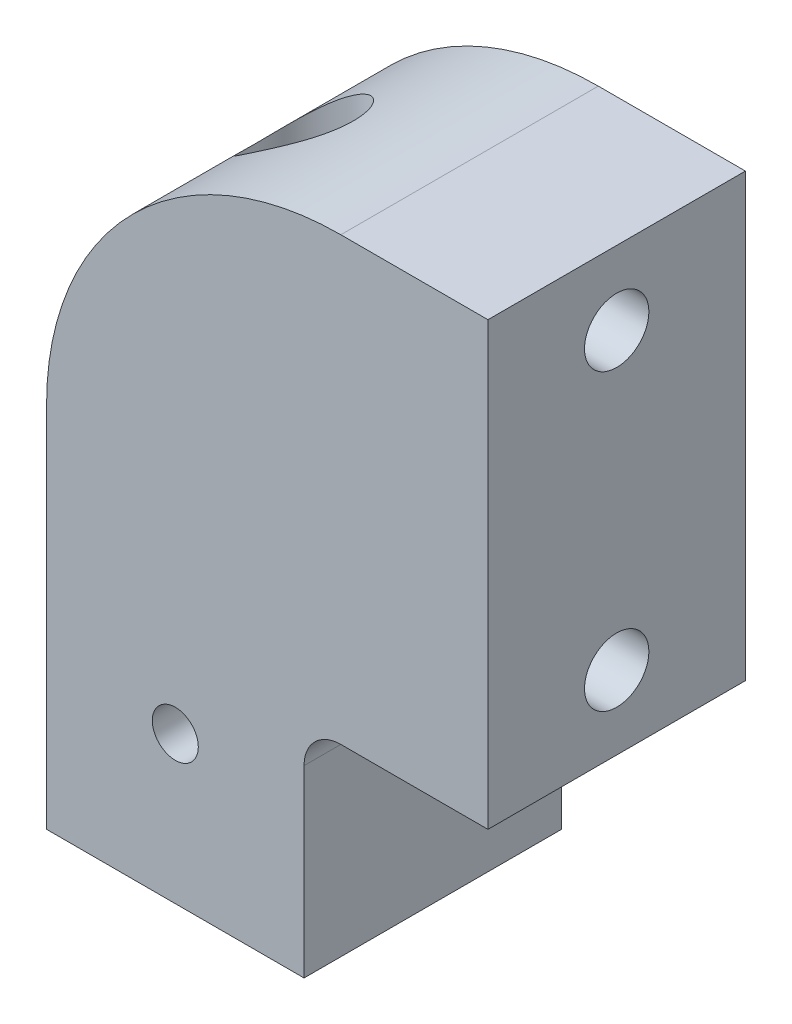
SolidWorks part; units mm, degrees
material "PE High Density"
ref_plane "Front Plane" through (0, 0, 0) normal (0, 0, 1) x (1, 0, 0)
ref_plane "Top Plane" through (0, 0, 0) normal (0, 1, 0) x (1, 0, 0)
ref_plane "Right Plane" through (0, 0, 0) normal (1, 0, 0) x (0, 0, -1)
sketch "Sketch1" plane through (0, 0, 0) normal (0, 0, 1) x (1, 0, 0)
  line L0 (0, 0) -> (0, 57.15)
  line L1 (38.1, 57.15) -> (0, 57.15)
  line L2 (38.1, 57.15) -> (38.1, 19.05)
  line L3 (38.1, 19.05) -> (22.225, 19.05)
  line L4 (22.225, 19.05) -> (22.225, 0)
  line L5 (22.225, 0) -> (0, 0)
  dimension "D1" = 22.225
  dimension "D2" = 19.05
  dimension "D3" = 38.1
  dimension "D4" = 38.1
extrude "Boss-Extrude1" add sketch "Sketch1" along normal blind 22.225
fillet "Fillet1" radius 3.175 1 edges at (22.225, 19.05, 11.1125)
fillet "Fillet2" radius 25.4 1 edges at (0, 57.15, 11.1125)
sketch "Sketch3" plane through (0, 0, 0) normal (0, -1, 0) x (1, 0, 0)
  line L0 (0, 22.225) -> (22.225, 0) construction
  line L1 (0, 0) -> (22.225, 0) construction
  line L2 (22.225, 0) -> (22.225, 22.225) construction
  line L3 (22.225, 22.225) -> (0, 0) construction
  circle A0 centre (11.1125, 11.1125) radius 7.1438
  dimension "D1" = 14.2875
extrude "Cut-Extrude1" cut sketch "Sketch3" against normal blind 9.525
sketch "Sketch4" plane through (0, 0, 0) normal (0, -1, 0) x (1, 0, 0)
  circle A0 centre (11.1125, 11.1125) radius 4.25
  dimension "D1" = 8.5
extrude "Cut-Extrude2" cut sketch "Sketch4" against normal through all
hole_wizard "7/32 (0.21875) Diameter Hole1" positions "Sketch7" profile "Sketch5" hole size "7/32" standard "ANSI Inch"
sketch "Sketch7" plane through (38.1, 0, 0) normal (1, 0, 0) x (0, 0, -1)
  line L0 (-11.1125, 57.15) -> (-11.1125, 19.05) construction
  line L1 (-22.225, 57.15) -> (0, 57.15) construction
  line L2 (-22.225, 19.05) -> (0, 19.05) construction
  line L4 (-22.225, 38.1) -> (0, 38.1) construction
  line L5 (-22.225, 19.05) -> (-22.225, 57.15) construction
  line L6 (0, 19.05) -> (0, 57.15) construction
  point P0 (-11.1125, 50.8)
  point P2 (-11.1125, 25.4)
  dimension "D1" = 25.4
sketch "Sketch5" plane through (38.1, 50.8, 11.1125) normal (0, 1, 0) x (0, 0, -1)
  line L0 (0, 0) -> (0, 9.6068)
  line L1 (0, 9.6068) -> (2.7781, 7.9375)
  line L2 (2.7781, 7.9375) -> (2.7781, 0)
  line L5 (2.7781, 0) -> (0, 0)
  line L10 (0, 9.6068) -> (-2.7781, 7.9375) construction
  line L11 (0, -6.35) -> (0, 107.95) construction
  dimension "Hole Dia." = 5.5562
  dimension "Hole Depth" = 7.9375
  dimension "Drill Angle" = 118
sketch "Sketch9" plane through (22.225, 0, 0) normal (1, 0, 0) x (0, 0, -1)
  line L0 (-11.1125, 0) -> (-11.1125, 12.7) construction
  line L1 (-22.225, 0) -> (0, 0) construction
  circle A0 centre (-11.1125, 12.7) radius 1.9844
  dimension "D1" = 3.9688
  dimension "D2" = 12.7
extrude "Cut-Extrude3" cut sketch "Sketch9" against normal through all
sketch "Sketch10" plane through (0, 0, 22.225) normal (0, 0, 1) x (1, 0, 0)
  line L0 (11.1125, 0) -> (11.1125, 12.7) construction
  line L1 (0, 0) -> (22.225, 0) construction
  circle A0 centre (11.1125, 12.7) radius 1.9844
  dimension "D1" = 3.9688
  dimension "D2" = 12.7
extrude "Cut-Extrude4" cut sketch "Sketch10" against normal through all
